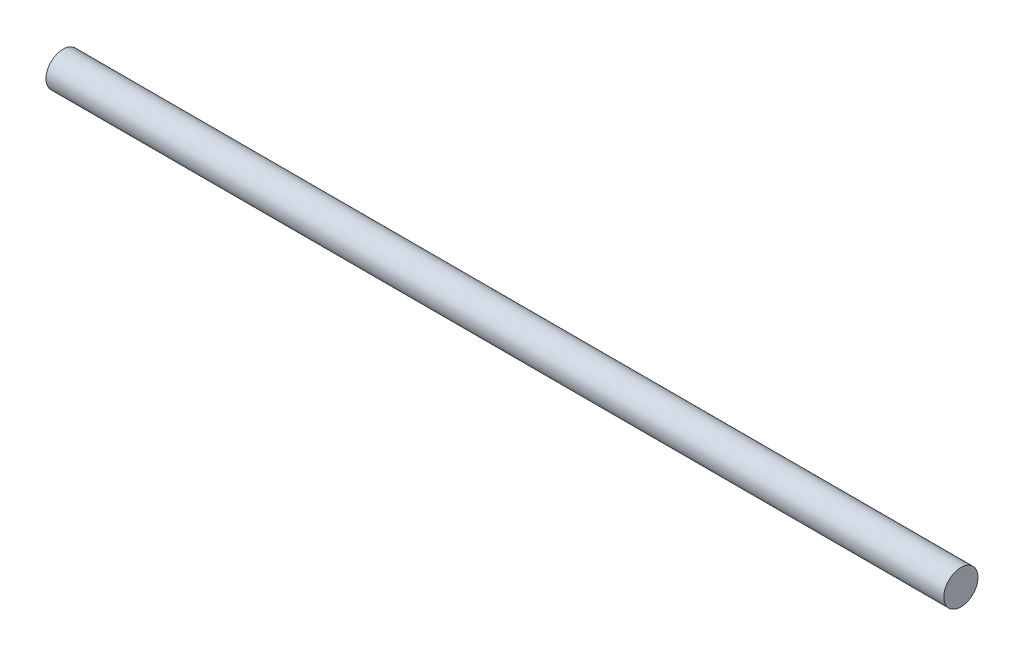
SolidWorks part; units mm, degrees
ref_plane "Front Plane" through (0, 0, 0) normal (0, 0, 1) x (1, 0, 0)
ref_plane "Top Plane" through (0, 0, 0) normal (0, 1, 0) x (1, 0, 0)
ref_plane "Right Plane" through (0, 0, 0) normal (1, 0, 0) x (0, 0, -1)
sketch "Sketch1" plane through (0, 0, 0) normal (1, 0, 0) x (0, 0, -1)
  circle A0 centre (0, 0) radius 4.7625
  dimension "D1" = 9.525
extrude "Boss-Extrude1" add sketch "Sketch1" along normal blind 250
